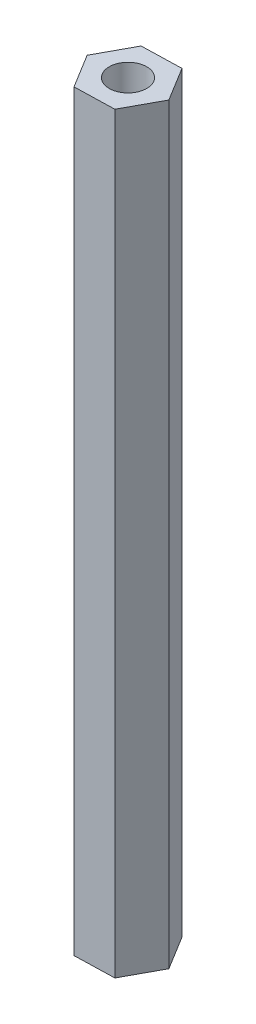
SolidWorks part; units mm, degrees
material "Латунь"
ref_plane "Спереди" through (0, 0, 0) normal (0, 0, 1) x (1, 0, 0)
ref_plane "Сверху" through (0, 0, 0) normal (0, 1, 0) x (1, 0, 0)
ref_plane "Справа" through (0, 0, 0) normal (1, 0, 0) x (0, 0, -1)
sketch "Эскиз1" plane through (0, 0, 0) normal (0, 1, 0) x (1, 0, 0)
  line L1 (-1.5144, -2.791) -> (1.6599, -2.707)
  line L2 (1.6599, -2.707) -> (3.1743, 0.084)
  line L3 (3.1743, 0.084) -> (1.5144, 2.791)
  line L4 (1.5144, 2.791) -> (-1.6599, 2.707)
  line L5 (-1.6599, 2.707) -> (-3.1743, -0.084)
  line L6 (-3.1743, -0.084) -> (-1.5144, -2.791)
  circle A0 centre (0, 0) radius 2.75 construction
  dimension "D1" = 5.5
extrude "Бобышка-Вытянуть1" add sketch "Эскиз1" along normal blind 60
sketch "Эскиз2" plane through (0, 60, 0) normal (0, 1, 0) x (1, 0, 0)
  circle A0 centre (0, 0) radius 1.5
  dimension "D1" = 3
extrude "Вырез-Вытянуть1" cut sketch "Эскиз2" against normal blind 10
sketch "Эскиз3" plane through (0, 0, 0) normal (0, -1, 0) x (1, 0, 0)
  circle A0 centre (0, 0) radius 1.5
  dimension "D1" = 3
extrude "Вырез-Вытянуть2" cut sketch "Эскиз3" against normal blind 10
